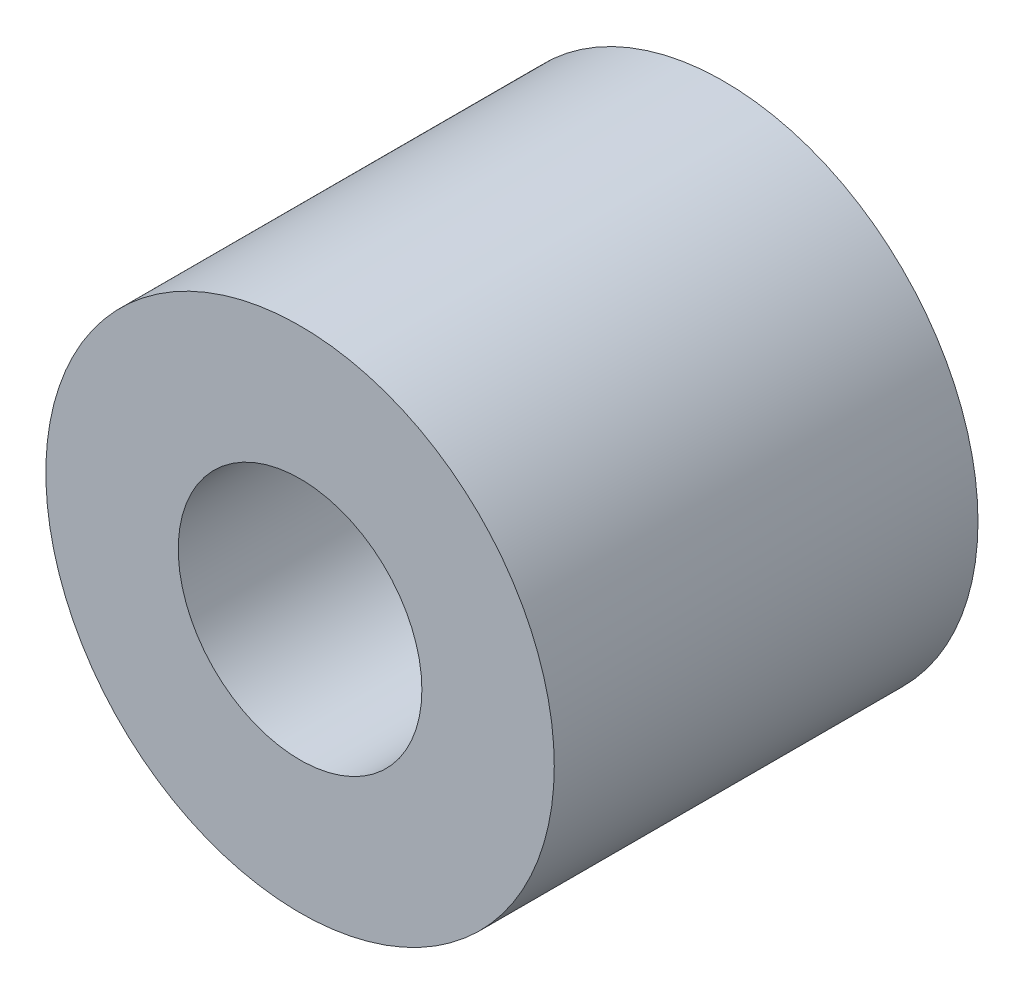
SolidWorks part; units mm, degrees
ref_plane "前视基准面" through (0, 0, 0) normal (0, 0, 1) x (1, 0, 0)
ref_plane "上视基准面" through (0, 0, 0) normal (0, 1, 0) x (1, 0, 0)
ref_plane "右视基准面" through (0, 0, 0) normal (1, 0, 0) x (0, 0, -1)
sketch "草图1" plane through (0, 0, 0) normal (0, 0, 1) x (1, 0, 0)
  circle A0 centre (0, 0) radius 1.15
  circle A1 centre (0, 0) radius 2.4
extrude "凸台-拉伸2" add sketch "草图1" along normal blind 4
